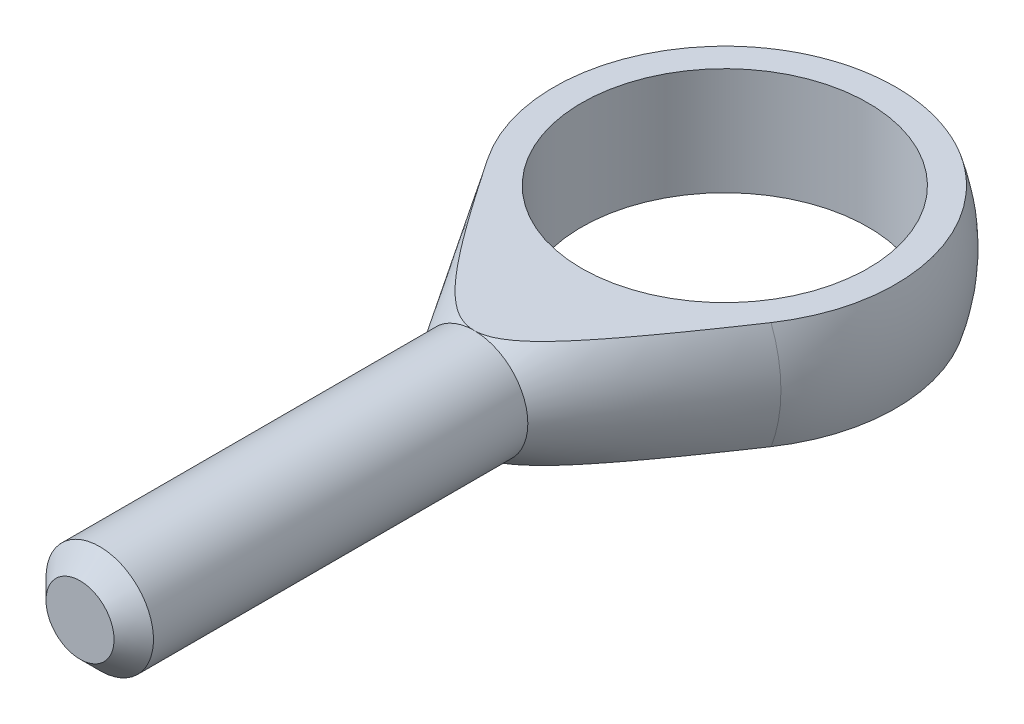
SolidWorks part; units mm, degrees
material "1.0545 (S355N)"
ref_plane "Płaszczyzna przednia" through (0, 0, 0) normal (0, 0, 1) x (1, 0, 0)
ref_plane "Płaszczyzna górna" through (0, 0, 0) normal (0, 1, 0) x (1, 0, 0)
ref_plane "Płaszczyzna prawa" through (0, 0, 0) normal (1, 0, 0) x (0, 0, -1)
sketch "Szkic1" plane through (0, 0, 0) normal (0, 1, 0) x (1, 0, 0)
  line L0 (0, 26.0435) -> (0, -71.4286) construction
  line L1 (-3, -36) -> (3, -36)
  line L2 (3, -36) -> (3, -14)
  line L3 (-3, -36) -> (-3, -14)
  line L4 (-8.4613, -5.3297) -> (-3, -14)
  line L5 (3, -14) -> (8.4613, -5.3297)
  line L6 (-3, -14) -> (3, -14)
  line L7 (0, 10) -> (0, -36)
  arc A0 (8.4613, -5.3297) -> (-8.4613, -5.3297) centre (0, 0) ccw
  point P7 (0, -36)
  dimension "d4" = 20
  dimension "d2" = 6
  dimension "l1" = 36
  dimension "l3" = 22
revolve "Obrót1" add sketch "Szkic1" angle 360 about L0
sketch "Szkic2" plane through (0, 0, 0) normal (1, 0, 0) x (0, 0, -1)
  line L4 (-14, 3) -> (9.5394, 3)
  line L5 (-14, -3) -> (9.5394, -3)
  line L6 (-14, -3) -> (-5.3297, -8.4613) construction
  line L7 (-5.3297, 8.4613) -> (-14, 3) construction
  line L8 (-14, -3) -> (-5.3297, -8.4613)
  line L9 (-5.3297, 8.4613) -> (-14, 3)
  arc A0 (-5.3297, -8.4613) -> (-5.3297, 8.4613) centre (0, 0) ccw construction
  arc A1 (-5.3297, -8.4613) -> (9.5394, -3) centre (0, 0) ccw
  arc A2 (9.5394, 3) -> (-5.3297, 8.4613) centre (0, 0) ccw
extrude "Wytnij-wyciągnięcie1" cut sketch "Szkic2" against normal through all both and the other way through all
sketch "Szkic3" plane through (0, 0, 0) normal (0, 1, 0) x (1, 0, 0)
  circle A0 centre (0, 0) radius 8
  dimension "b" = 16
extrude "Wytnij-wyciągnięcie2" cut sketch "Szkic3" against normal through all both and the other way through all contours A0
chamfer "Sfazowanie1" distance 1.1 angle 45 1 edges at (-3, 0, 36)
equation "\"D1@Sfazowanie1\"=\"l3@Szkic1\"*0.05"
